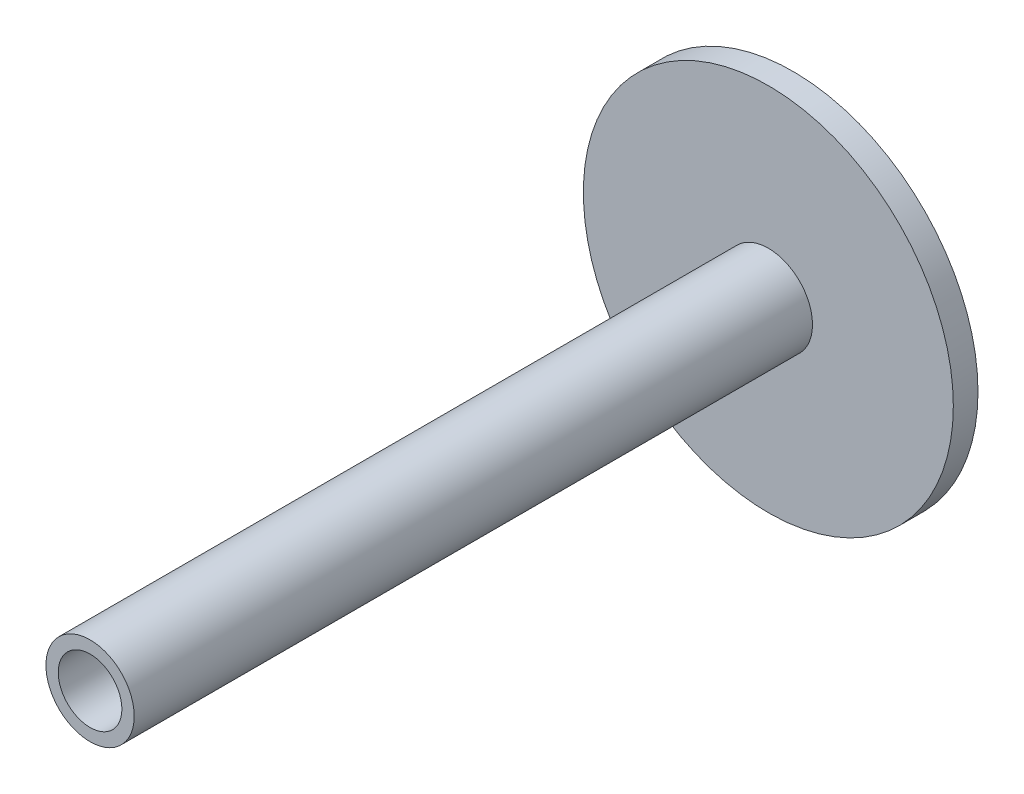
SolidWorks part; units mm, degrees
ref_plane "Front Plane" through (0, 0, 0) normal (0, 0, 1) x (1, 0, 0)
ref_plane "Top Plane" through (0, 0, 0) normal (0, 1, 0) x (1, 0, 0)
ref_plane "Right Plane" through (0, 0, 0) normal (1, 0, 0) x (0, 0, -1)
sketch "Sketch1" plane through (0, 0, 0) normal (0, 0, 1) x (1, 0, 0)
  circle A0 centre (0, 0) radius 15
  dimension "D1" = 30
extrude "Boss-Extrude1" add sketch "Sketch1" along normal blind 2
sketch "Sketch2" plane through (0, 0, 2) normal (0, 0, 1) x (1, 0, 0)
  circle A0 centre (0, 0) radius 2.58
  circle A1 centre (0, 0) radius 3.58
  dimension "D1" = 5.16
  dimension "D2" = 7.16
extrude "Boss-Extrude2" add sketch "Sketch2" along normal blind 55
sketch "Sketch3" plane through (0, 0, 2) normal (0, 0, 1) x (1, 0, 0)
  circle A0 centre (0, 0) radius 2.58
extrude "Cut-Extrude1" cut sketch "Sketch3" against normal blind 55
